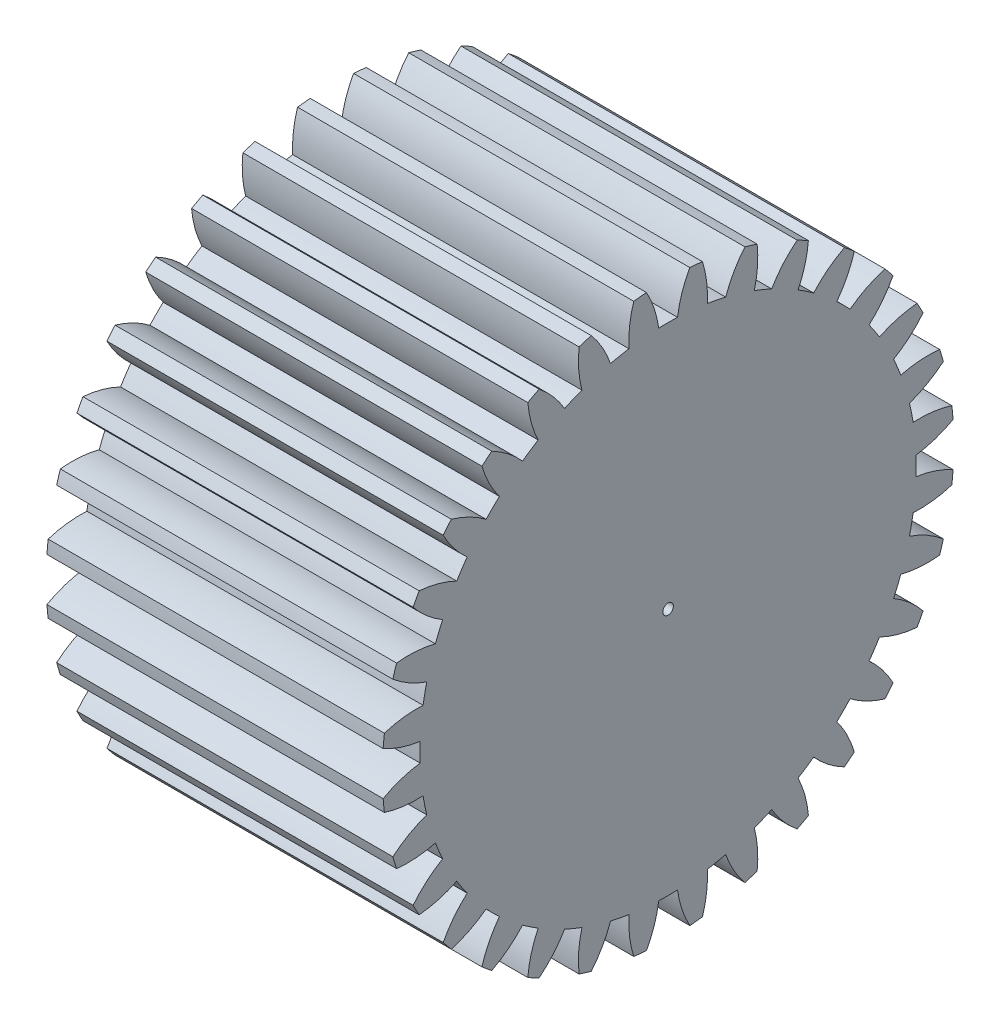
SolidWorks part; units mm, degrees
ref_plane "Plane1" through (0, 0, 0) normal (0, 0, 1) x (1, 0, 0)
ref_plane "Plane2" through (0, 0, 0) normal (0, 1, 0) x (1, 0, 0)
ref_plane "Plane3" through (0, 0, 0) normal (1, 0, 0) x (0, 0, -1)
other "Configuration Table"
sketch "HoldingSke" plane through (0, 0, 0) normal (0, 1, 0) x (1, 0, 0)
  line L0 (0, 0) -> (430.8084, -269.199)
  line L1 (-15, 0) -> (100, 0) construction
  line L2 (0, 0) -> (-2.1039, 2.3779)
  line L3 (0, 0) -> (-11.863, 4.5341)
  line L4 (0, 0) -> (7.3237, 4.5764)
  line L5 (0, 0) -> (-47.5972, -17.7524)
  line L6 (0, 0) -> (-21.0557, -14.2063)
  line L7 (-2.1039, 2.3779) -> (8.8308, 51.9871)
  line L8 (-76.2, 54.61) -> (-75.184, 54.61)
  line L9 (-67.7845, 28.3722) -> (-49.3413, 33.142)
  line L10 (-76.2, 71.12) -> (104.1128, 71.12)
  line L11 (0, 0) -> (-25.4, 0)
  line L12 (-76.2, 101.6) -> (-76.1492, 101.6)
  line L13 (24.9733, 27.94) -> (52.9518, 28.4284)
  line L14 (24.9733, 27.94) -> (25.0241, 27.9398)
  line L15 (24.9733, 27.94) -> (100.4021, 29.52)
  circle A0 centre (0, 0) radius 0.3969
  circle A1 centre (0, 0) radius 18.7452
  circle A2 centre (0, 0) radius 38.1
  circle A3 centre (0, 0) radius 0.3969
  dimension "MHD" = 37.4904
  dimension "Hub_dia" = 76.2
  dimension "Bore" = 0.7937
  dimension "MBD" = 0.7937
  dimension "Num_teeth" = 32
  dimension "Pitch" = 508
  dimension "Overall_len" = 50.8
  dimension "Show_teeth" = 32
  dimension "Thickness" = 25.4
  dimension "OAL" = 50.8001
  dimension "T_dim" = 1.016
  dimension "Ap" = 14.5
  dimension "H" = 19.05
  dimension "Pitch_radius" = 180.3128
  dimension "Width" = 25.4
  dimension "Backlash" = 0.0508
  dimension "Addendum_fac" = 1
  dimension "Dedendum_fac" = 1.2
  dimension "Clearance_fac" = 0.2
  dimension "Dedendum_add" = 0.0508
sketch "BasProSke" plane through (0, 0, 0) normal (0, 1, 0) x (1, 0, 0)
  line L0 (-10, 0) -> (60, 0) construction
  line L1 (0, 0) -> (0, 21.59)
  line L2 (0, 0) -> (25.4, 0)
  line L3 (25.4, 0) -> (25.4, 21.59)
  line L4 (25.4, 21.59) -> (0, 21.59)
  dimension "Thickness" = 25.4
  dimension "Diameter" = 43.18
revolve "Base-Revolve" add sketch "BasProSke" angle 360 about L0
sketch "TooCutSke" plane through (0, 0, 0) normal (1, 0, 0) x (0, 0, -1)
  line L1 (0, 0) -> (0, 107) construction
  line L2 (0, 0) -> (-1.0859, 20.291) construction
  line L3 (0, 0) -> (-3.9794, 40.4039) construction
  line L4 (-1.0859, 20.291) -> (-1.9897, 20.2019) construction
  arc A0 (0.7098, 18.7318) -> (-0.7098, 18.7318) centre (0, 0) ccw
  arc A1 (1.6502, 21.5523) -> (-1.6502, 21.5523) centre (0, 0) ccw
  circle A2 centre (0, 0) radius 20.32 construction
  circle A3 centre (0, 0) radius 19.6728 construction
  arc A4 (-0.7098, 18.7318) -> (-1.6502, 21.5523) centre (-8.7606, 17.6145) ccw
  arc A5 (1.6502, 21.5523) -> (0.7098, 18.7318) centre (8.7606, 17.6145) ccw
  dimension "Root_dia" = 37.4904
  dimension "Overcut_dia" = 43.2308
  dimension "Pitch_dia" = 40.64
  dimension "Base_dia" = 39.3455
  dimension "Flank_rad" = 8.128
  dimension "Half_ang" = 5.625
  dimension "Half_CT" = 0.9082
extrude "ToothCut" cut sketch "TooCutSke" along normal through all
fillet "Breaks" [suppressed] radius 0.0254
fillet "RootFillets" [suppressed] radius 0.3048
pattern_circular "TeethCuts" count 32 every 11.25 about axis through (-10, 0, 0) along (1, 0, 0) of "ToothCut", "RootFillets", "Breaks"
sketch "HubNeaOneSke" plane through (0, 0, 0) normal (-1, 0, 0) x (0, 0, 1)
  circle A0 centre (0, 0) radius 18.7452
  dimension "Diameter" = 37.4904
extrude "HubNearOne" [suppressed] add sketch "HubNeaOneSke" along normal blind 25.4001
sketch "HubNeaBotSke" plane through (0, 0, 0) normal (-1, 0, 0) x (0, 0, 1)
  circle A0 centre (0, 0) radius 18.7452
  dimension "Diameter" = 37.4904
extrude "HubNearBoth" [suppressed] add sketch "HubNeaBotSke" along normal blind 12.7
ref_plane "FarPln" through (25.4, 0, 0) normal (1, 0, 0) x (0, 0, -1)
sketch "HubFarSke" plane through (25.4, 0, 0) normal (1, 0, 0) x (0, 0, -1)
  circle A0 centre (0, 0) radius 18.7452
  dimension "Diameter" = 37.4904
extrude "HubFar" [suppressed] add sketch "HubFarSke" along normal blind 12.7
sketch "BorSke" plane through (0, 0, 0) normal (1, 0, 0) x (0, 0, -1)
  circle A0 centre (0, 0) radius 0.3969
  dimension "Diameter" = 0.7937
extrude "Bore" cut sketch "BorSke" along normal mid plane 101.6001
sketch "KeySke" plane through (0, 0, 0) normal (1, 0, 0) x (0, 0, -1)
  line L0 (-0.127, 0) -> (-0.127, 0.6191)
  line L1 (-0.127, 0.6191) -> (0.127, 0.6191)
  line L2 (0.127, 0.6191) -> (0.127, 0)
  line L3 (0, 0) -> (0, 34) construction
  line L4 (-0.127, 0) -> (0.127, 0)
  dimension "Offset" = 0.6191
  dimension "Width" = 0.254
extrude "Keyway" [suppressed] cut sketch "KeySke" along normal mid plane 101.6001
pattern_circular "Keyway2" [suppressed] count 2 every 90 about axis through (-10, 0, 0) along (1, 0, 0)
equation "' \"Pitch@HoldingSke\" = 4"
equation "' \"Num_teeth@HoldingSke\" = 12"
equation "' \"Ap@HoldingSke\" =  20"
equation "' \"Ap@HoldingSke\" = 20"
equation "' \"Width@HoldingSke\" = 0.5"
equation "' \"Hub_dia@HoldingSke\"= 1"
equation "' \"Hub_dia@HoldingSke\" = 1"
equation "' \"Overall_len@HoldingSke\" = 1.0"
equation "' \"Bore@HoldingSke\" = 0.75"
equation "' \"T_dim@HoldingSke\" = 0.85"
equation "' \"Width@KeySke\" = 0.25"
equation "' \"Show_teeth@HoldingSke\" = 13"
equation "' \"Backlash@HoldingSke\" = 0.009"
equation "' \"Addendum_fac@HoldingSke\" = 1.0"
equation "' \"Dedendum_fac@HoldingSke\" = 1.25"
equation "' \"Dedendum_add@HoldingSke\" = 0.00005"
equation "' \"Clearance_fac@HoldingSke\" = 0.25"
equation "' \"Pitch@HoldingSke\" = 0.5"
equation "' \"Num_teeth@HoldingSke\" = 23"
equation "' \"Show_teeth@HoldingSke\" = 23"
equation "' \"Backlash@HoldingSke\" = 0.0375"
equation "\"Overcut_dia@TooCutSke\" = (\"Num_teeth@HoldingSke\" + 2 * \"Addendum_fac@HoldingSke\") / \"Pitch@HoldingSke\" + 0.002"
equation "\"Pitch_dia@TooCutSke\" = \"Num_teeth@HoldingSke\" / \"Pitch@HoldingSke\""
equation "\"Base_dia@TooCutSke\" = \"Num_teeth@HoldingSke\" / \"Pitch@HoldingSke\" * cos((\"Ap@HoldingSke\"  * 3.14159265 / 180))"
equation "\"Root_dia@TooCutSke\" = (\"Num_teeth@HoldingSke\" + 2) / \"Pitch@HoldingSke\" - 2 * (\"Addendum_fac@HoldingSke\" + \"Dedendum_fac@HoldingSke\") / \"Pitch@HoldingSke\" - \"Dedendum_add@HoldingSke\" * 2"
equation "\"Half_ang@TooCutSke\" = 180 / \"Num_teeth@HoldingSke\""
equation "\"Half_CT@TooCutSke\" = \"Num_teeth@HoldingSke\" / \"Pitch@HoldingSke\" * sin((3.14159265 / 2 / \"Num_teeth@HoldingSke\")) / 2 - 7 * \"Backlash@HoldingSke\" / 4"
equation "\"Flank_rad@TooCutSke\" = \"Num_teeth@HoldingSke\" / \"Pitch@HoldingSke\" / 5"
equation "\"Radius@RootFillets\" = \"Clearance_fac@HoldingSke\" / \"Pitch@HoldingSke\" + \"Dedendum_add@HoldingSke\""
equation "\"Break_rad@Breaks\" = 0.02 / \"Pitch@HoldingSke\""
equation "\"Thickness@HoldingSke\" = \"Width@HoldingSke\""
equation "\"OAL@HoldingSke\" = \"Thickness@HoldingSke\""
equation "\"MHD@HoldingSke\" = (\"Num_teeth@HoldingSke\" + 2) / \"Pitch@HoldingSke\" - 2 * (\"Addendum_fac@HoldingSke\" + \"Dedendum_fac@HoldingSke\")  / \"Pitch@HoldingSke\" - \"Dedendum_add@HoldingSke\" * 2"
equation "\"MBD@HoldingSke\" = (\"Num_teeth@HoldingSke\" + 2) / \"Pitch@HoldingSke\" - 2 * (\"Addendum_fac@HoldingSke\" + \"Dedendum_fac@HoldingSke\")  / \"Pitch@HoldingSke\" - \"Dedendum_add@HoldingSke\" * 2 - 0.002"
equation "\"MHD@HoldingSke\" = ((sgn( \"MHD@HoldingSke\" - \"Hub_dia@HoldingSke\" )-1)*( \"MHD@HoldingSke\" - \"Hub_dia@HoldingSke\" ))/-2+ \"Hub_dia@HoldingSke\""
equation "\"MBD@HoldingSke\" = ((sgn( \"MBD@HoldingSke\" - \"Bore@HoldingSke\" )-1)*( \"MBD@HoldingSke\" - \"Bore@HoldingSke\" ))/-2+ \"Bore@HoldingSke\""
equation "\"OAL@HoldingSke\" = ((sgn( \"OAL@HoldingSke\" - \"Overall_len@HoldingSke\" )+1)*( \"OAL@HoldingSke\" - \"Overall_len@HoldingSke\" ))/2 + \"Overall_len@HoldingSke\" + 0.000002"
equation "\"Num_teeth@TeethCuts\" = int( \"Show_teeth@HoldingSke\" ) + 1"
equation "\"Num_teeth@TeethCuts\" = ((sgn( \"Num_teeth@TeethCuts\" - \"Num_teeth@HoldingSke\" )-1)*( \"Num_teeth@TeethCuts\" - \"Num_teeth@HoldingSke\" ))/-2+ \"Num_teeth@HoldingSke\""
equation "\"Num_teeth@TeethCuts\" = ((sgn( \"Num_teeth@TeethCuts\" - 2.0)+1)*( \"Num_teeth@TeethCuts\" - 2.0))/2 +2.0"
equation "\"Angle@TeethCuts\" = 360.0 / \"Num_teeth@HoldingSke\""
equation "\"Diameter@BasProSke\" = (\"Num_teeth@HoldingSke\" + 2 * \"Addendum_fac@HoldingSke\") / \"Pitch@HoldingSke\""
equation "\"Thickness@BasProSke\"  = \"Thickness@HoldingSke\""
equation "' \"Fillet_rad@BasProSke\" =  \"Thickness@HoldingSke\" * 0.05"
equation "' \"Fillet_rad@BasProSke\" = \"Thickness@HoldingSke\" * 0.05"
equation "\"MHD@HoldingSke\" = ((sgn( \"MHD@HoldingSke\" - \"Root_dia@TooCutSke\" )-1)*( \"MHD@HoldingSke\" - \"Root_dia@TooCutSke\" ))/-2+ \"Root_dia@TooCutSke\""
equation "\"Diameter@HubNeaOneSke\" = \"MHD@HoldingSke\""
equation "\"Length@HubNearOne\" = \"OAL@HoldingSke\" - \"Thickness@BasProSke\""
equation "\"Diameter@HubNeaBotSke\" = \"MHD@HoldingSke\""
equation "\"Length@HubNearBoth\" = ( \"OAL@HoldingSke\" - \"Thickness@BasProSke\" ) / 2.0"
equation "\"Thickness@FarPln\" = \"Thickness@BasProSke\""
equation "\"Diameter@HubFarSke\" = \"MHD@HoldingSke\""
equation "\"Length@HubFar\" = ( \"OAL@HoldingSke\" - \"Thickness@BasProSke\" ) / 2.0"
equation "\"Diameter@BorSke\" = \"MBD@HoldingSke\""
equation "\"D1@Bore\" = \"OAL@HoldingSke\" * 2.0"
equation "\"D1@Keyway\" = \"OAL@HoldingSke\" * 2.0"
equation "\"Offset@KeySke\" = \"T_dim@HoldingSke\" - \"MBD@HoldingSke\" / 2.0"
